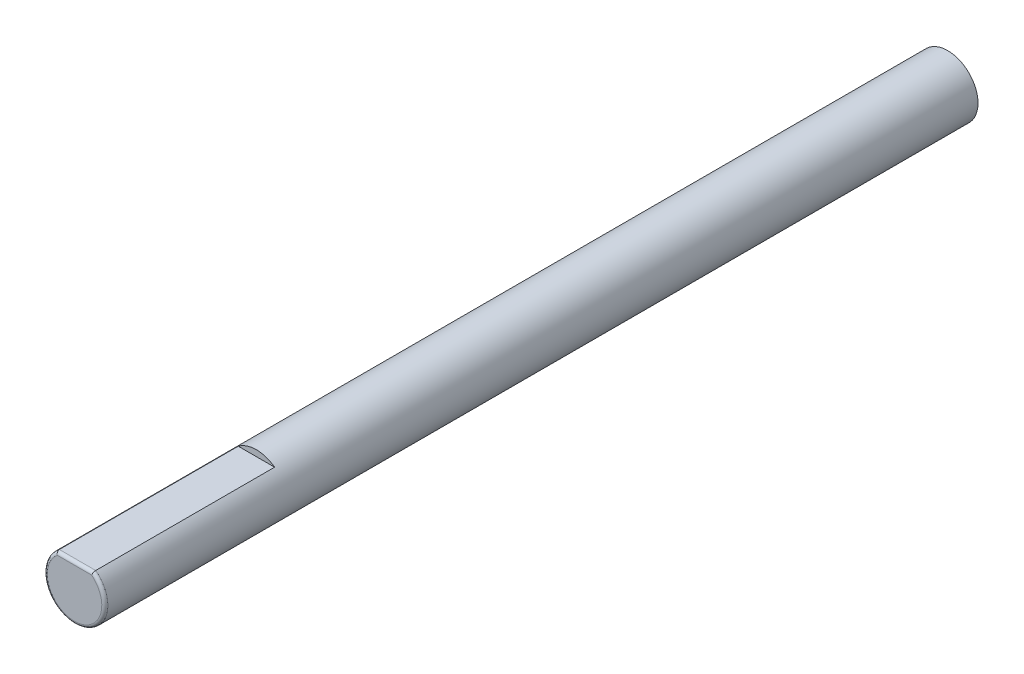
SolidWorks part; units mm, degrees
ref_plane "Front Plane" through (0, 0, 0) normal (0, 0, 1) x (1, 0, 0)
ref_plane "Top Plane" through (0, 0, 0) normal (0, 1, 0) x (1, 0, 0)
ref_plane "Right Plane" through (0, 0, 0) normal (1, 0, 0) x (0, 0, -1)
sketch "Sketch1" plane through (0, 0, 0) normal (0, 0, 1) x (1, 0, 0)
  circle A0 centre (0, 0) radius 2.5
  dimension "D1" = 5
extrude "Shaft Body" add sketch "Sketch1" along normal mid plane 72
sketch "Sketch2" plane through (0, 0, 36) normal (0, 0, 1) x (1, 0, 0)
  line L0 (-1.5, 2) -> (1.5, 2)
  line L1 (0, 2.5) -> (3, 2.5) construction
  circle A1 centre (0, 0) radius 2.5 construction
  arc A2 (1.5, 2) -> (-1.5, 2) centre (0, 0) ccw
  point P6 (0, 2.5)
  point P7 (3.8224, 2.5)
  dimension "D1" = 3
  dimension "D2" = 0.5
extrude "D Cut" cut sketch "Sketch2" against normal blind 15
fillet "Fillet" radius 0.25 2 edges at (0, -2.5, 36) (0, 2, 36)
